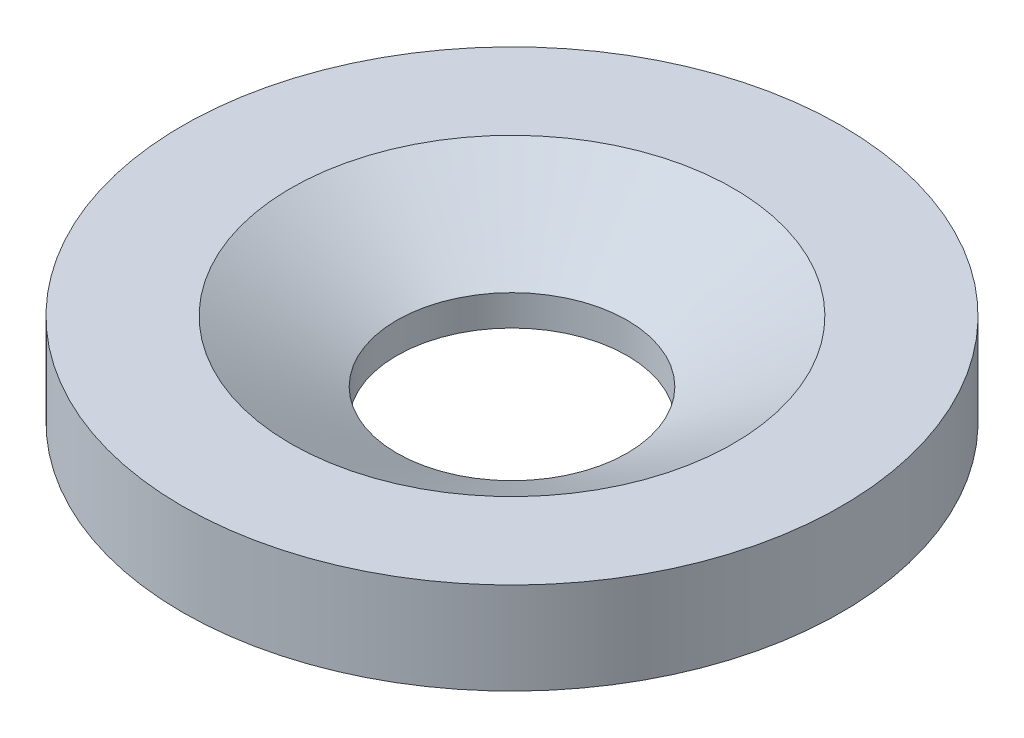
SolidWorks part; units mm, degrees
ref_plane "Front Plane" through (0, 0, 0) normal (0, 0, 1) x (1, 0, 0)
ref_plane "Top Plane" through (0, 0, 0) normal (0, 1, 0) x (1, 0, 0)
ref_plane "Right Plane" through (0, 0, 0) normal (1, 0, 0) x (0, 0, -1)
sketch "Sketch1" plane through (0, 0, 0) normal (0, 0, 1) x (1, 0, 0)
  line L0 (47.752, 0) -> (47.752, 12.7)
  line L1 (47.752, 0) -> (136.652, 0)
  line L2 (47.752, 12.7) -> (91.7461, 38.1)
  line L3 (101.2599, 12.7) -> (-8.6018, 12.7) construction
  line L4 (136.652, 0) -> (136.652, 38.1)
  line L5 (91.7461, 38.1) -> (136.652, 38.1)
  line L6 (0, 36.5441) -> (0, -32.6716) construction
  dimension "D1" = 12.7
  dimension "D2" = 88.9
  dimension "D3" = 30
  dimension "D4" = 38.1
revolve "Revolve1" add sketch "Sketch1" angle 360 about L6
